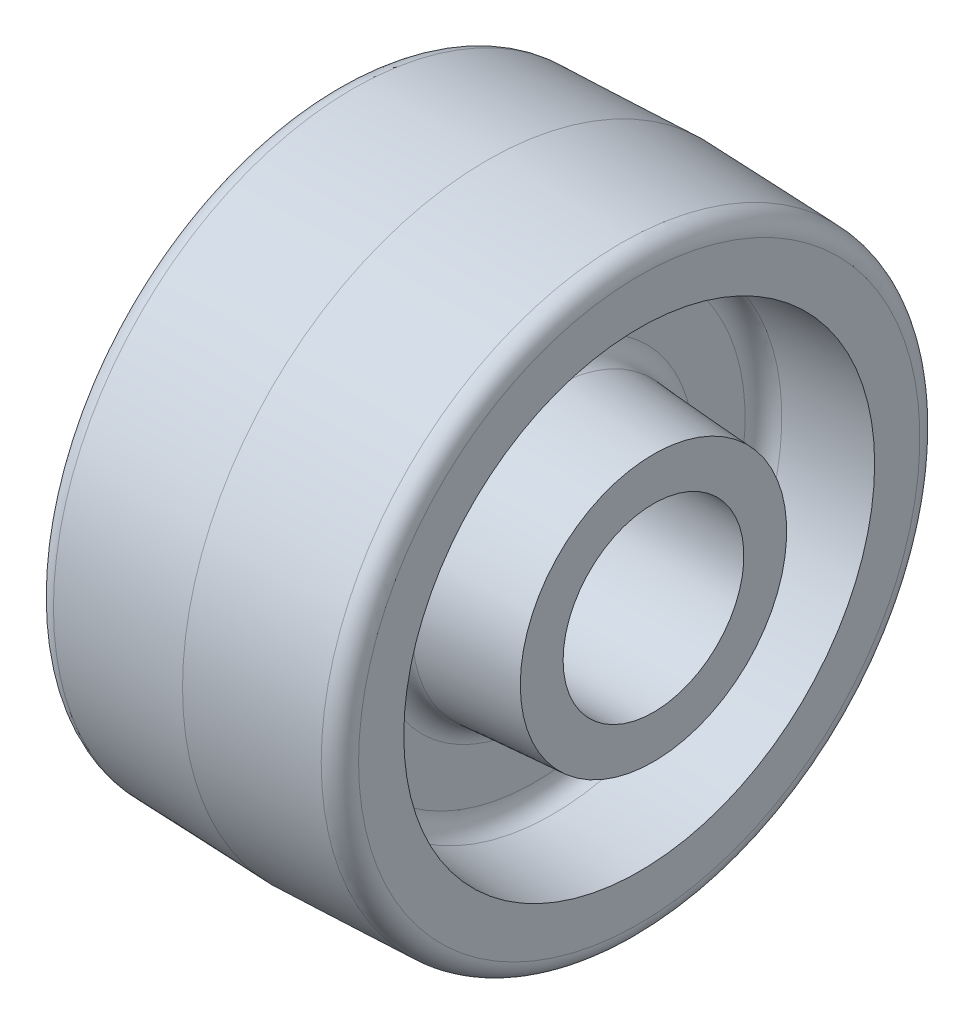
SolidWorks part; units mm, degrees
ref_plane "Plano frontal" through (0, 0, 0) normal (0, 0, 1) x (1, 0, 0)
ref_plane "Plano superior" through (0, 0, 0) normal (0, 1, 0) x (1, 0, 0)
ref_plane "Plano direito" through (0, 0, 0) normal (1, 0, 0) x (0, 0, -1)
ref_plane "Plano1" through (0, 0, 0) normal (0, 0, 1) x (1, 0, 0)
sketch "Esboço1" plane through (0, 0, 0) normal (0, 0, 1) x (1, 0, 0)
  line L0 (-27.7812, 0) -> (-27.7812, 22.225)
  line L1 (-27.7812, 22.225) -> (-10.8977, 23.3701)
  line L2 (-7.9375, 26.5378) -> (-7.9375, 35.133)
  line L3 (-10.8977, 38.3008) -> (-25.4, 39.2844)
  line L4 (-25.4, 39.2844) -> (-25.4, 46.8274)
  line L5 (-22.3386, 50.0004) -> (0, 50.8)
  line L6 (0, 50.8) -> (22.3386, 50.0004)
  line L7 (25.4, 46.8274) -> (25.4, 39.2844)
  line L8 (25.4, 39.2844) -> (10.8977, 38.3008)
  line L9 (7.9375, 35.133) -> (7.9375, 26.5378)
  line L10 (10.8977, 23.3701) -> (27.7812, 22.225)
  line L11 (27.7812, 22.225) -> (27.7812, 0)
  line L12 (27.7812, 0) -> (-27.7812, 0)
  line L13 (27.7812, 0) -> (-27.7812, 0) construction
  arc A0 (-10.8977, 23.3701) -> (-7.9375, 26.5378) centre (-11.1125, 26.5378) ccw
  arc A1 (-7.9375, 35.133) -> (-10.8977, 38.3008) centre (-11.1125, 35.133) ccw
  arc A2 (-25.4, 46.8274) -> (-22.3386, 50.0004) centre (-22.225, 46.8274) cw
  arc A3 (22.3386, 50.0004) -> (25.4, 46.8274) centre (22.225, 46.8274) cw
  arc A4 (10.8977, 38.3008) -> (7.9375, 35.133) centre (11.1125, 35.133) ccw
  arc A5 (7.9375, 26.5378) -> (10.8977, 23.3701) centre (11.1125, 26.5378) ccw
revolve "Revolução1" add sketch "Esboço1" angle 360 about L13
ref_plane "Plano2" through (0, 0, 0) normal (0, 0, 1) x (1, 0, 0)
sketch "Esboço2" plane through (0, 0, 0) normal (0, 0, 1) x (1, 0, 0)
  line L0 (-30.5594, 0) -> (-30.5594, 15.0812)
  line L1 (-30.5594, 15.0812) -> (30.5594, 15.0812)
  line L2 (30.5594, 15.0812) -> (30.5594, 0)
  line L3 (30.5594, 0) -> (-30.5594, 0)
  line L4 (30.5594, 0) -> (-30.5594, 0) construction
revolve "Corte-Revolução1" cut sketch "Esboço2" angle 360 about L4
